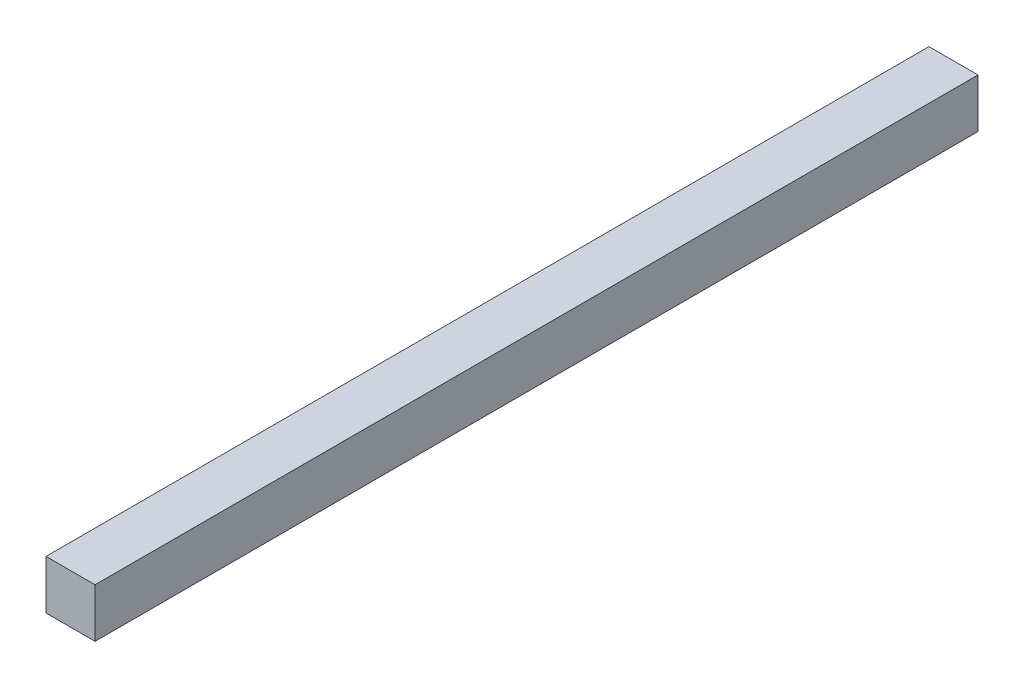
SolidWorks part; units mm, degrees
ref_plane "Plan de face" through (0, 0, 0) normal (0, 0, 1) x (1, 0, 0)
ref_plane "Plan de dessus" through (0, 0, 0) normal (0, 1, 0) x (1, 0, 0)
ref_plane "Plan de droite" through (0, 0, 0) normal (1, 0, 0) x (0, 0, -1)
sketch "Esquisse1" plane through (0, 0, 0) normal (0, 0, 1) x (1, 0, 0)
  line L1 (-7.5, -7.5) -> (7.5, -7.5)
  line L2 (-7.5, -7.5) -> (-7.5, 7.5)
  line L3 (-7.5, 7.5) -> (7.5, 7.5)
  line L4 (7.5, -7.5) -> (7.5, 7.5)
  line L5 (-7.5, -7.5) -> (7.5, 7.5) construction
  line L6 (-7.5, 7.5) -> (7.5, -7.5) construction
  point P0 (0, 0)
  dimension "D1" = 15
  dimension "D2" = 15
extrude "Boss.-Extru.1" add sketch "Esquisse1" along normal blind 270
